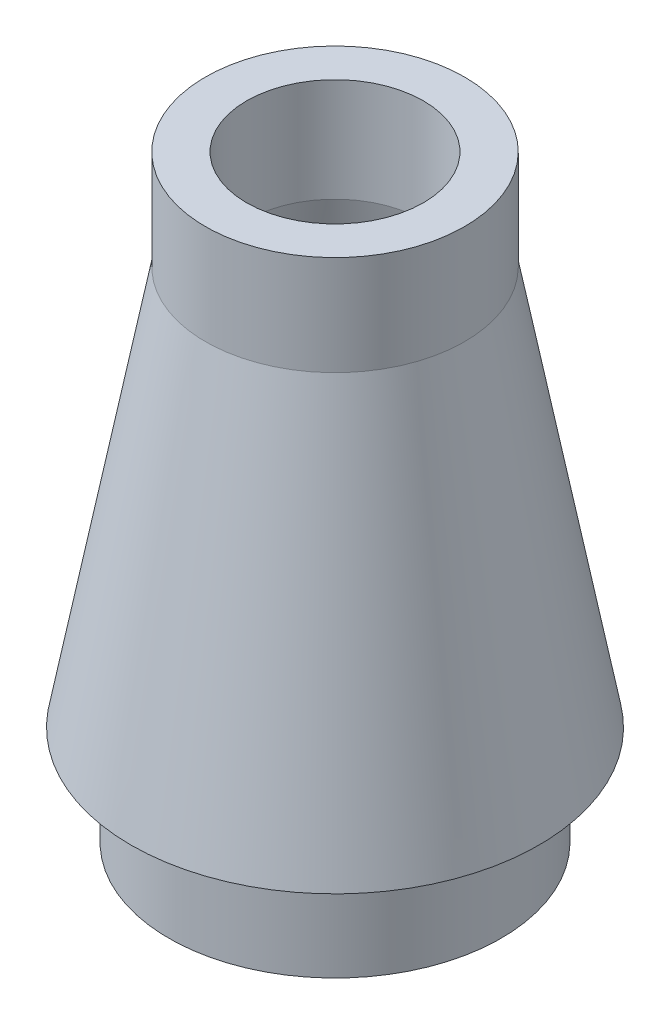
SolidWorks part; units mm, degrees
ref_plane "Front Plane" through (0, 0, 0) normal (0, 0, 1) x (1, 0, 0)
ref_plane "Top Plane" through (0, 0, 0) normal (0, 1, 0) x (1, 0, 0)
ref_plane "Right Plane" through (0, 0, 0) normal (1, 0, 0) x (0, 0, -1)
sketch "Sketch1" plane through (0, 0, 0) normal (0, 0, 1) x (1, 0, 0)
  line L0 (0, 0) -> (0, 11.43) construction
  line L1 (0, 11.43) -> (-2.4765, 11.43)
  line L2 (-2.4765, 11.43) -> (-2.4765, 9.525)
  line L3 (-2.4765, 9.525) -> (-3.8989, 1.905)
  line L4 (-3.8989, 1.905) -> (-3.175, 1.905)
  line L5 (-3.175, 1.905) -> (-3.175, 0)
  line L6 (-3.175, 0) -> (0, 0)
  line L7 (0, 0) -> (0, 11.43)
  dimension "D1" = 11.43
  dimension "D2" = 9.525
  dimension "D3" = 1.905
  dimension "D4" = 6.35
  dimension "D5" = 7.7978
  dimension "D6" = 4.953
revolve "Revolve1" add sketch "Sketch1" angle 360 about L0
shell "Shell1" thickness 0.7874
